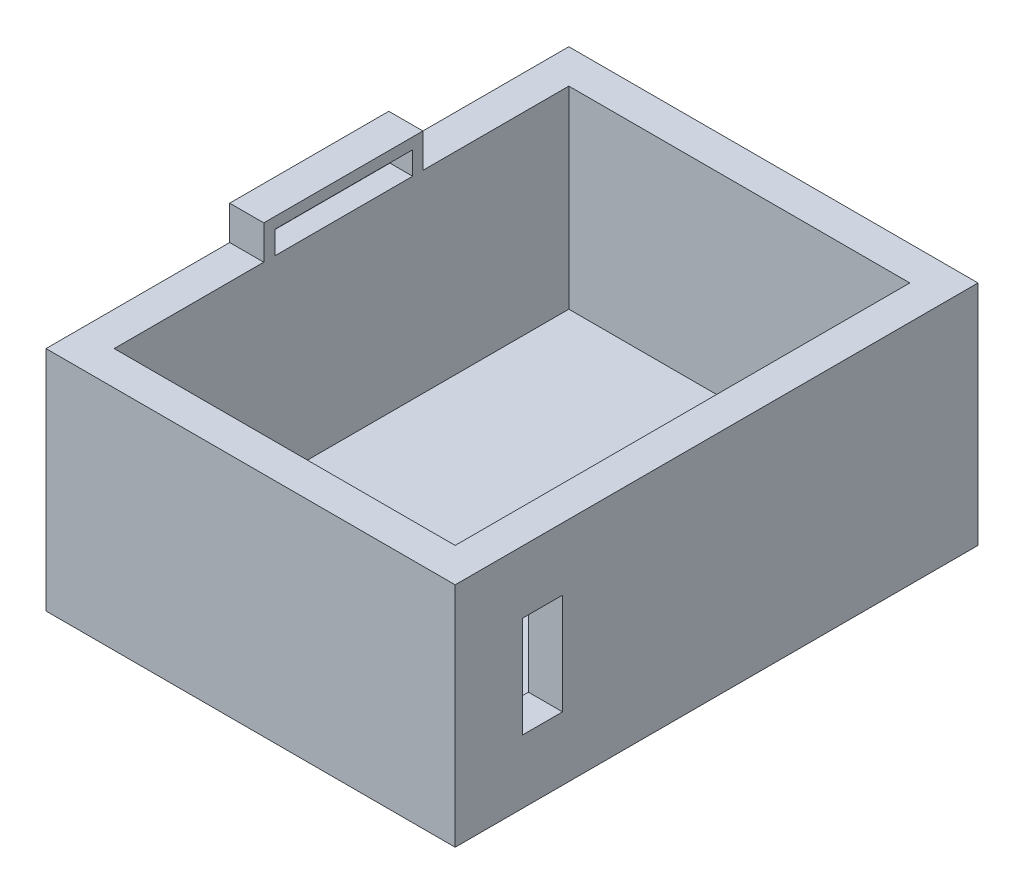
SolidWorks part; units mm, degrees
ref_plane "Front Plane" through (0, 0, 0) normal (0, 0, 1) x (1, 0, 0)
ref_plane "Top Plane" through (0, 0, 0) normal (0, 1, 0) x (1, 0, 0)
ref_plane "Right Plane" through (0, 0, 0) normal (1, 0, 0) x (0, 0, -1)
sketch "Sketch1" plane through (0, 0, 0) normal (0, 1, 0) x (1, 0, 0)
  line L1 (-75, 100) -> (75, 100)
  line L2 (-75, 100) -> (-75, -100)
  line L3 (-75, -100) -> (75, -100)
  line L4 (75, 100) -> (75, -100)
  line L5 (-75, 100) -> (75, -100) construction
  line L6 (-75, -100) -> (75, 100) construction
  line L7 (-90, 115) -> (90, 115)
  line L8 (-90, 115) -> (-90, -115)
  line L9 (-90, -115) -> (90, -115)
  line L10 (90, 115) -> (90, -115)
  line L11 (-90, 115) -> (90, -115) construction
  line L12 (-90, -115) -> (90, 115) construction
  point P0 (0, 0)
  point P6 (0, 0)
  point P11 (0, -100)
  point P12 (0, -115)
  dimension "D1" = 150
  dimension "D2" = 200
  dimension "D3" = 15
  dimension "D4" = 15
extrude "Boss-Extrude1" add sketch "Sketch1" along normal blind 100
sketch "Sketch2" plane through (0, 0, 0) normal (0, -1, 0) x (1, 0, 0)
  line L2 (-90, 115) -> (90, 115)
  line L3 (-90, 115) -> (-90, -115)
  line L4 (-90, -115) -> (90, -115)
  line L5 (90, 115) -> (90, -115)
extrude "Boss-Extrude2" add sketch "Sketch2" against normal blind 15
sketch "Sketch3" plane through (0, 100, 0) normal (0, 1, 0) x (1, 0, 0)
  line L1 (-75, -100) -> (-75, 100) construction
  line L2 (-90, 35.8015) -> (-75, 35.8015)
  line L3 (-90, 35.8015) -> (-90, -34.1985)
  line L4 (-90, -34.1985) -> (-75, -34.1985)
  line L6 (-75, 35.8015) -> (-75, -34.1985)
  line L7 (-90, 35.8015) -> (-75, -34.1985) construction
  line L8 (-90, -34.1985) -> (-75, 35.8015) construction
  line L9 (-90, 115) -> (-90, -115) construction
  point P0 (-82.5, 0.8015)
  dimension "D1" = 70
extrude "Boss-Extrude3" add sketch "Sketch3" along normal blind 15
sketch "Sketch4" plane through (-75, 0, 0) normal (1, 0, 0) x (0, 0, -1)
  line L0 (-115, 100) -> (115, 100) construction
  line L1 (-29.2234, 110.1021) -> (31.3015, 110.1021)
  line L2 (-29.2234, 110.1021) -> (-29.2234, 100)
  line L3 (-29.2234, 100) -> (31.3015, 100)
  line L4 (31.3015, 110.1021) -> (31.3015, 100)
extrude "Cut-Extrude1" cut sketch "Sketch4" against normal blind 10
sketch "Sketch5" plane through (90, 0, 0) normal (1, 0, 0) x (0, 0, -1)
  line L1 (-85.4584, 72.4585) -> (-67.7684, 72.4585)
  line L2 (-85.4584, 72.4585) -> (-85.4584, 27.9733)
  line L3 (-85.4584, 27.9733) -> (-67.7684, 27.9733)
  line L4 (-67.7684, 72.4585) -> (-67.7684, 27.9733)
extrude "Cut-Extrude2" cut sketch "Sketch5" against normal blind 20
